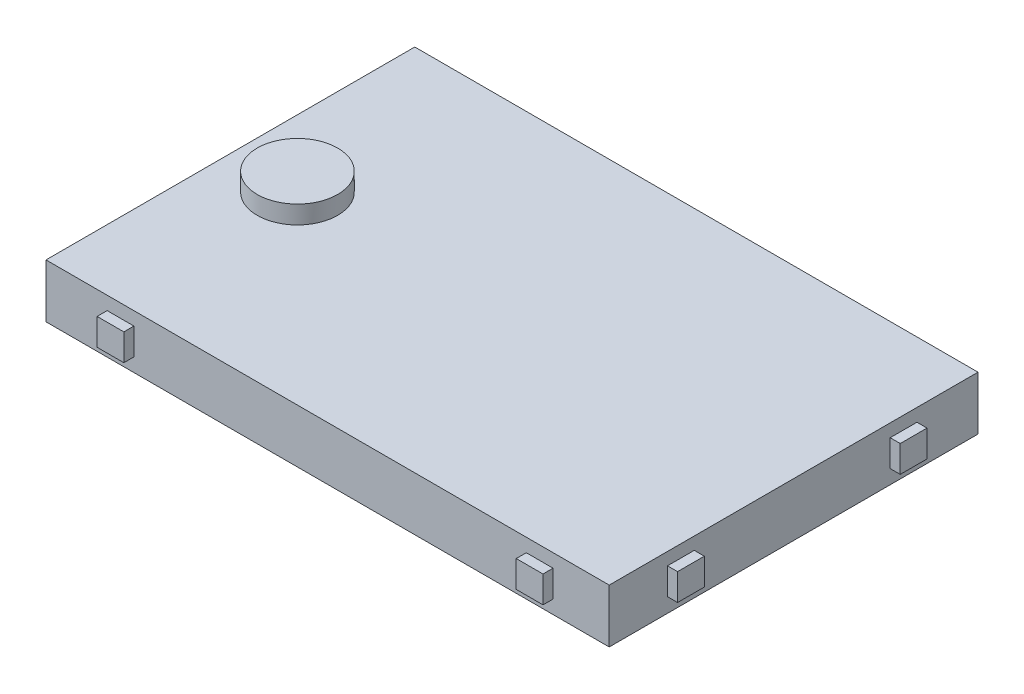
SolidWorks part; units mm, degrees
ref_plane "Front Plane" through (0, 0, 0) normal (0, 0, 1) x (1, 0, 0)
ref_plane "Top Plane" through (0, 0, 0) normal (0, 1, 0) x (1, 0, 0)
ref_plane "Right Plane" through (0, 0, 0) normal (1, 0, 0) x (0, 0, -1)
sketch "Sketch1" plane through (0, 0, 0) normal (0, 1, 0) x (1, 0, 0)
  line L1 (-42, -27.5) -> (42, -27.5)
  line L2 (-42, -27.5) -> (-42, 27.5)
  line L3 (-42, 27.5) -> (42, 27.5)
  line L4 (42, -27.5) -> (42, 27.5)
  line L5 (-42, -27.5) -> (42, 27.5) construction
  line L6 (-42, 27.5) -> (42, -27.5) construction
  point P0 (0, 0)
  dimension "D1" = 84
  dimension "D2" = 55
extrude "Boss-Extrude1" add sketch "Sketch1" along normal blind 8
sketch "Sketch2" plane through (0, -0.4392, 27.5) normal (0, 0, 1) x (1, 0, 0)
  line L1 (-28.8909, 2.4617) -> (-32.8782, 2.4617)
  line L2 (-28.8909, 2.4617) -> (-28.8909, 6.449)
  line L3 (-28.8909, 6.449) -> (-32.8782, 6.449)
  line L4 (-32.8782, 2.4617) -> (-32.8782, 6.449)
  line L5 (-28.8909, 2.4617) -> (-32.8782, 6.449) construction
  line L6 (-28.8909, 6.449) -> (-32.8782, 2.4617) construction
  point P0 (-30.8846, 4.4553)
  dimension "D1" = 3.9873
  dimension "D2" = 3.9873
extrude "Boss-Extrude2" add sketch "Sketch2" along normal blind 1.5
sketch "Sketch3" plane through (0, -0.5903, 27.5) normal (0, 0, 1) x (1, 0, 0)
  line L1 (33.6227, 2.5943) -> (29.6327, 2.5943)
  line L2 (33.6227, 2.5943) -> (33.6227, 6.5843)
  line L3 (33.6227, 6.5843) -> (29.6327, 6.5843)
  line L4 (29.6327, 2.5943) -> (29.6327, 6.5843)
  line L5 (33.6227, 2.5943) -> (29.6327, 6.5843) construction
  line L6 (33.6227, 6.5843) -> (29.6327, 2.5943) construction
  point P0 (31.6277, 4.5893)
  dimension "D1" = 3.99
  dimension "D2" = 3.99
extrude "Boss-Extrude3" add sketch "Sketch3" along normal blind 1.5
sketch "Sketch6" plane through (42, 0.1014, -1.5059) normal (1, 0, 0) x (0, 0, -1)
  line L1 (-16.3224, 2.049) -> (-20.3124, 2.049)
  line L2 (-16.3224, 2.049) -> (-16.3224, 6.039)
  line L3 (-16.3224, 6.039) -> (-20.3124, 6.039)
  line L4 (-20.3124, 2.049) -> (-20.3124, 6.039)
  line L5 (-16.3224, 2.049) -> (-20.3124, 6.039) construction
  line L6 (-16.3224, 6.039) -> (-20.3124, 2.049) construction
  point P0 (-18.3174, 4.044)
  dimension "D1" = 3.99
  dimension "D2" = 3.99
extrude "Boss-Extrude4" add sketch "Sketch6" along normal blind 1.5
sketch "Sketch7" plane through (42, -0.062, -3.1149) normal (1, 0, 0) x (0, 0, -1)
  line L1 (15.2786, 2.1551) -> (11.2886, 2.1551)
  line L2 (15.2786, 2.1551) -> (15.2786, 6.1451)
  line L3 (15.2786, 6.1451) -> (11.2886, 6.1451)
  line L4 (11.2886, 2.1551) -> (11.2886, 6.1451)
  line L5 (15.2786, 2.1551) -> (11.2886, 6.1451) construction
  line L6 (15.2786, 6.1451) -> (11.2886, 2.1551) construction
  point P0 (13.2836, 4.1501)
  dimension "D1" = 3.99
  dimension "D2" = 3.99
extrude "Boss-Extrude5" add sketch "Sketch7" along normal blind 1.5
sketch "Sketch4" plane through (0, 0, 27.5) normal (0, 0, 1) x (1, 0, 0)
  line L0 (-42, 4) -> (42, 4)
  line L1 (-42, 8) -> (-42, 0) construction
  line L2 (42, 8) -> (42, 0) construction
sketch "Sketch8" plane through (42, 0, 0) normal (1, 0, 0) x (0, 0, -1)
  line L0 (-27.5, 4) -> (27.5, 4) construction
  line L2 (27.5, 8) -> (27.5, 0) construction
  point P3 (0, 4)
sketch "Sketch9" plane through (0, 8, 0) normal (0, 1, 0) x (1, 0, 0)
  line L0 (-42, 0) -> (-32, 0)
  line L1 (-42, 27.5) -> (-42, -27.5) construction
  dimension "D1" = 10
sketch "Sketch10" plane through (0, 8, 0) normal (0, 1, 0) x (1, 0, 0)
  circle A0 centre (-32, 0) radius 6
extrude "Boss-Extrude6" add sketch "Sketch10" along normal blind 2.7
